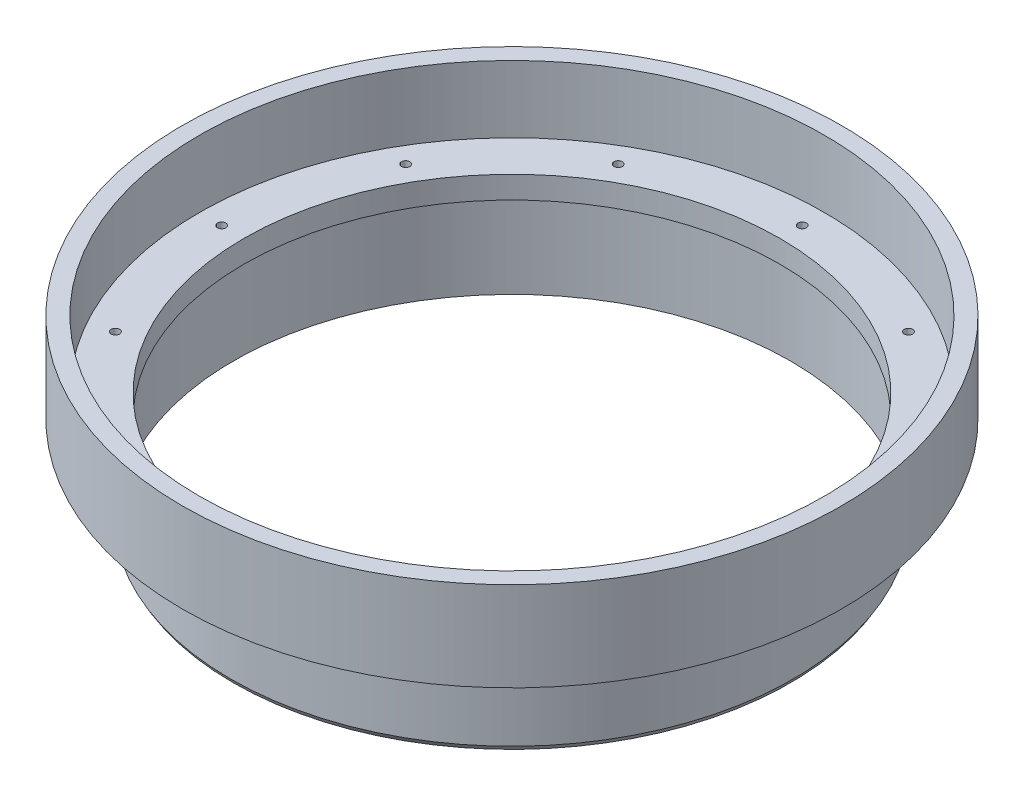
SolidWorks part; units mm, degrees
material "6061-T6 (SS)"
ref_plane "Front Plane" through (0, 0, 0) normal (0, 0, 1) x (1, 0, 0)
ref_plane "Top Plane" through (0, 0, 0) normal (0, 1, 0) x (1, 0, 0)
ref_plane "Right Plane" through (0, 0, 0) normal (1, 0, 0) x (0, 0, -1)
ref_axis "Axis1" through (0, 55, 0) along (0, -1, 0)
sketch "Cross Section" plane through (0, 0, 0) normal (0, 0, 1) x (1, 0, 0)
  line L0 (-38.1, 0) -> (-38.1, -3.175)
  line L1 (-38.1, -3.175) -> (-39.624, -3.175)
  line L2 (-39.624, -3.175) -> (-39.624, -15.875)
  line L3 (-39.624, -15.875) -> (-40.005, -15.2151)
  line L4 (0, -15.875) -> (-38.1, -15.875) construction
  line L5 (-40.005, -15.2151) -> (-40.005, -3.175)
  line L6 (-40.005, -3.175) -> (-46.863, -3.175)
  line L7 (-46.863, -3.175) -> (-46.863, 9.525)
  line L8 (-46.863, 9.525) -> (-44.45, 9.525)
  line L9 (-44.45, 9.525) -> (-44.45, 0)
  line L10 (-44.45, 0) -> (-38.1, 0)
  line L11 (-38.1, 0) -> (0, 0) construction
  line L12 (0, 55) -> (0, -55) construction
  line L14 (-44.45, 1.5875) -> (-44.45, 3.175) construction
  dimension "D1" = 1.524
  dimension "D3" = 0.381
  dimension "D4" = 30
  dimension "D5" = 6.858
  dimension "D6" = 12.7
  dimension "D9" = 3.175
  dimension "D8" = 38.1
revolve "Main" add sketch "Cross Section" angle 360 about axis through (0, 55, 0) along (0, -1, 0)
sketch "Hole Location" plane through (0, 0, 0) normal (0, 1, 0) x (1, 0, 0)
  line L0 (0, 0) -> (-41.275, 0) construction
  circle A0 centre (0, 0) radius 41.275 construction
  dimension "D1" = 82.55
hole_wizard "#0-80 Tapped Hole1" positions "Sketch5" profile "Sketch7" tap size "#0-80" standard "ANSI Inch"
sketch "Sketch5" plane through (0, 0, 0) normal (0, 1, 0) x (1, 0, 0)
  point P0 (-41.275, 0)
sketch "Sketch7" plane through (-41.275, 0, 0) normal (1, 0, 0) x (0, 0, 1)
  line L0 (0, 0) -> (0, 3.5329)
  line L1 (0, 3.5329) -> (0.5956, 3.175)
  line L2 (0.5956, 3.175) -> (0.5956, 0)
  line L5 (0.5956, 0) -> (0, 0)
  line L10 (0, 3.5329) -> (-0.5956, 3.175) construction
  line L11 (0, -6.35) -> (0, 107.95) construction
  dimension "Tap Drill Dia." = 1.1913
  dimension "Tap Drill Depth" = 3.175
  dimension "Drill Angle" = 118
cosmetic thread "Hole Thread1" parameters "D1"=3.048, "D2"=1.524
pattern_circular "Screw Holes" count 12 over 360 about axis through (0, 0, 0) along (0, 1, 0) of "#0-80 Tapped Hole1"
equation "\"D8@Cross Section\"=\"TANK DIAMETER@Cryo Tank.SLDASM\"/2"
equation "\"D1@Hole Location\"=\"TANK DIAMETER@Cryo Tank.SLDASM\"+\"GASKET SEAT THICKNESS@Cryo Tank.SLDASM\""
equation "\"D1@Cross Section\"=\"LINER THICKNESS@Cryo Tank.SLDASM\""
equation "\"D3@Cross Section\"=\"ALUMINUM LAP THICKNESS@Cryo Tank.SLDASM\""
equation "\"D5@Cross Section\"=2*\"CF THICKNESS@Cryo Tank.SLDASM\"+\"NOMEX THICKNESS@Cryo Tank.SLDASM\""
